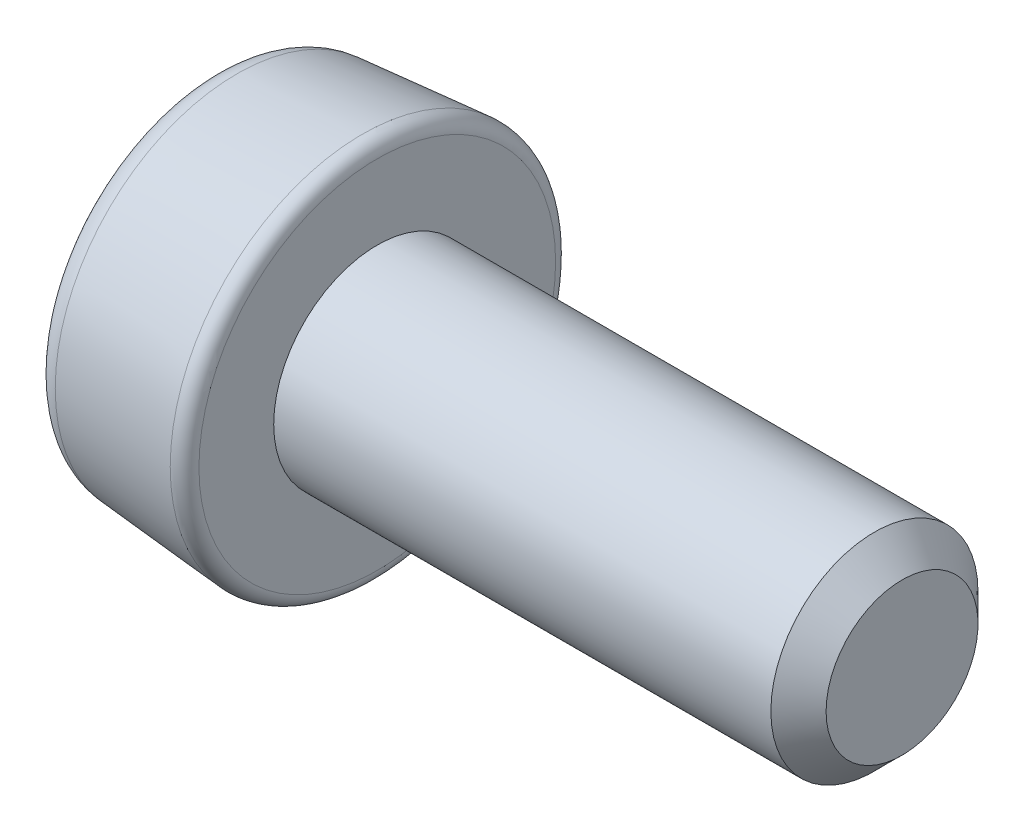
SolidWorks part; units mm, degrees
material "Acier allié inoxydable"
ref_plane "Plan de face" through (0, 0, 0) normal (0, 0, 1) x (1, 0, 0)
ref_plane "Plan de dessus" through (0, 0, 0) normal (0, 1, 0) x (1, 0, 0)
ref_plane "Plan de droite" through (0, 0, 0) normal (1, 0, 0) x (0, 0, -1)
sketch "Esquisse1" plane through (0, 0, 0) normal (0, 0, 1) x (1, 0, 0)
  line L0 (-2.7839, 0) -> (5.865, 0) construction
  line L1 (3.8, 0) -> (3.8, 0.55)
  line L2 (3.8, 0.55) -> (3.6, 0.75)
  line L3 (3.6, 0.75) -> (0, 0.75)
  line L4 (0, 0.75) -> (0, 1.2913)
  line L5 (-0.1083, 1.391) -> (-1.0166, 1.3153)
  line L6 (-1.2, 1.116) -> (-1.2, 0)
  line L7 (-1.2, 0) -> (3.8, 0)
  arc A0 (-1.2, 1.116) -> (-1.0166, 1.3153) centre (-1, 1.116) cw
  arc A1 (-0.1083, 1.391) -> (0, 1.2913) centre (-0.1, 1.2913) cw
  point P12 (-1.2, 1.3)
  point P15 (0, 1.4)
  dimension "D8" = 0.2
  dimension "D9" = 0.1
  dimension "D1" = 0.75
  dimension "D2" = 3.8
  dimension "D3" = 3.6
  dimension "D4" = 1.3
  dimension "D5" = 1.2
  dimension "D6" = 135
  dimension "D7" = 1.4
revolve "Révolution1" add sketch "Esquisse1" angle 360 about L0
sketch "Esquisse2" plane through (-1.2, 0, 0) normal (-1, 0, 0) x (0, 0, 1)
  line L1 (-0.15, 0) -> (0.15, 0)
  line L2 (-0.15, 0) -> (-0.15, 0.7)
  line L3 (-0.15, 0.7) -> (0.15, 0.7)
  line L4 (0.15, 0) -> (0.15, 0.7)
  dimension "D1" = 0.3
  dimension "D2" = 0.7
extrude "Extrusion1" cut sketch "Esquisse2" against normal blind 0.8
pattern_circular "Répétition circulaire1" count 4 over 360 about axis through (0, 0, 0) along (1, 0, 0) of "Extrusion1"
chamfer "Chanfrein1" distance 0.2 angle 45 4 edges at (-0.8, 0.15, 0.15) (-0.8, -0.15, 0.15) (-0.8, -0.15, -0.15) (-0.8, 0.15, -0.15)
